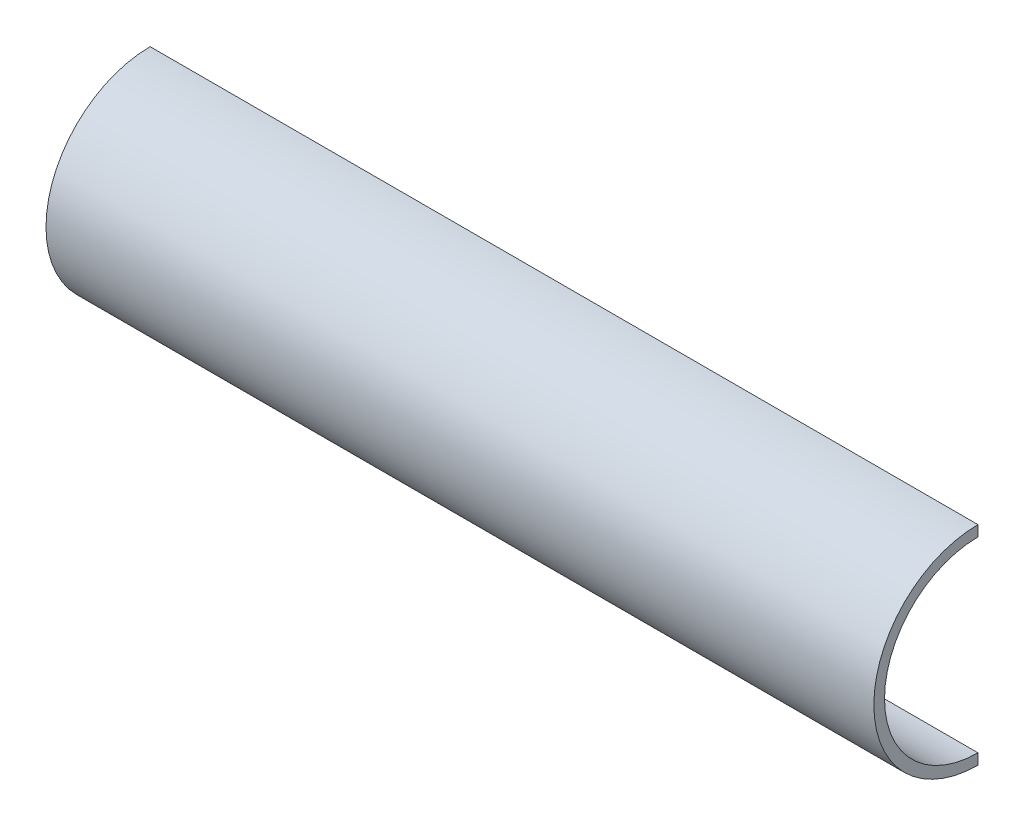
SolidWorks part; units mm, degrees
material "ABS"
ref_plane "Front Plane" through (0, 0, 0) normal (0, 0, 1) x (1, 0, 0)
ref_plane "Top Plane" through (0, 0, 0) normal (0, 1, 0) x (1, 0, 0)
ref_plane "Right Plane" through (0, 0, 0) normal (1, 0, 0) x (0, 0, -1)
sketch "Sketch1" plane through (0, 0, 0) normal (1, 0, 0) x (0, 0, -1)
  line L0 (0, 35) -> (7, 35)
  line L1 (7, 35) -> (7, -35)
  line L2 (7, -35) -> (0, -35)
  line L3 (0, 39) -> (7, 39)
  line L4 (7, 39) -> (7, 35)
  line L5 (0, -39) -> (7, -39)
  line L6 (7, -39) -> (7, -35)
  line L7 (0, -39) -> (0, 39)
  line L9 (-35, 0) -> (7, 0) construction
  circle A0 centre (0, 0) radius 35
  circle A1 centre (0, 0) radius 39
  dimension "D1" = 70
  dimension "D3" = 4
  dimension "D2" = 7
extrude "Boss-Extrude1" add sketch "Sketch1" along normal blind 310 contours L7 A1 A0
